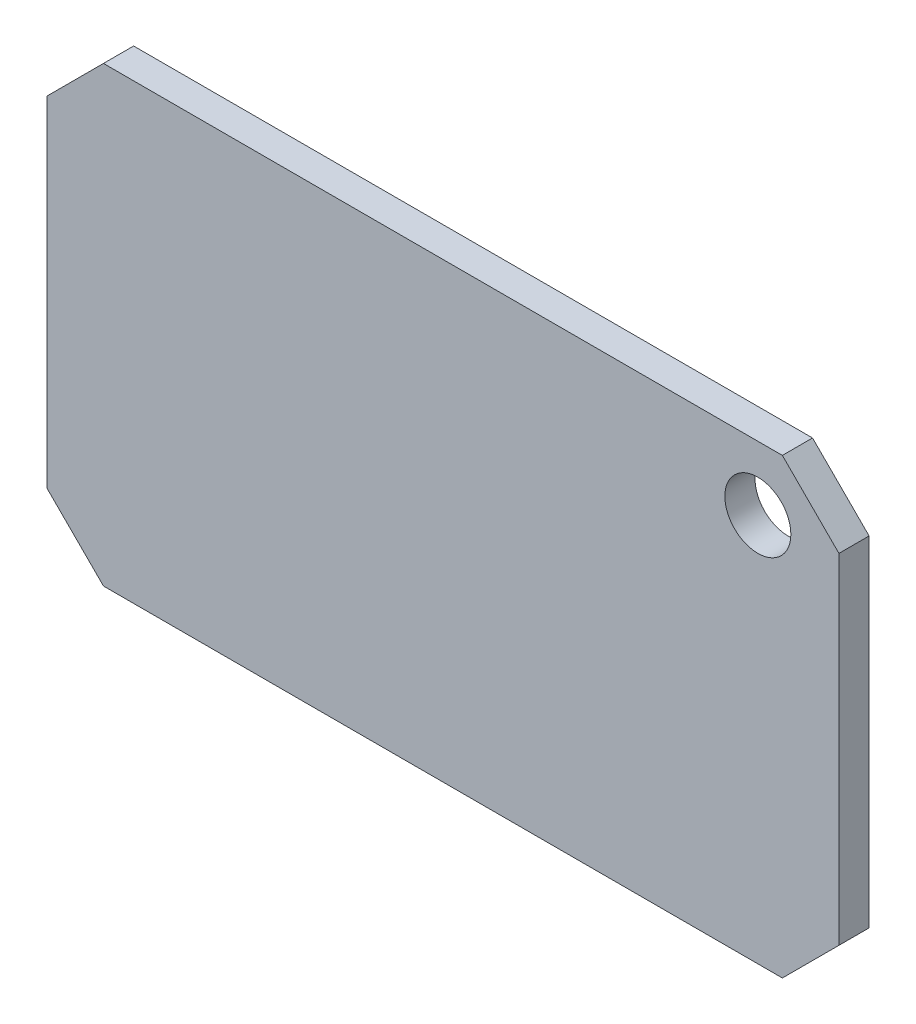
SolidWorks part; units mm, degrees
ref_plane "Front Plane" through (0, 0, 0) normal (0, 0, 1) x (1, 0, 0)
ref_plane "Top Plane" through (0, 0, 0) normal (0, 1, 0) x (1, 0, 0)
ref_plane "Right Plane" through (0, 0, 0) normal (1, 0, 0) x (0, 0, -1)
sketch "Sketch1" plane through (0, 0, 0) normal (0, 0, 1) x (1, 0, 0)
  line L0 (0, 0) -> (0, 12) construction
  line L1 (0, 0) -> (-21, 0) construction
  line L5 (-21, 9) -> (-18, 12)
  line L6 (-18, 12) -> (18, 12)
  line L7 (18, 12) -> (21, 9)
  line L8 (21, 9) -> (21, -9)
  line L9 (21, -9) -> (18, -12)
  line L10 (18, -12) -> (-18, -12)
  line L11 (-18, -12) -> (-21, -9)
  line L12 (-21, -9) -> (-21, 9)
  line L15 (18, 12) -> (18, -12) construction
  line L16 (-18, 12) -> (-18, -12) construction
  line L17 (-21, -9) -> (21, -9) construction
  line L18 (21, 9) -> (-21, 9) construction
  line L19 (0, 0) -> (21, 0) construction
  circle A0 centre (16.7, 8.6) radius 1.75
  dimension "D9" = 3.5
  dimension "D1" = 45
  dimension "D3" = 24
  dimension "D5" = 42
  dimension "D6" = 3
  dimension "D7" = 4.3
  dimension "D8" = 3.4
extrude "Boss-Extrude1" add sketch "Sketch1" along normal blind 1.6
